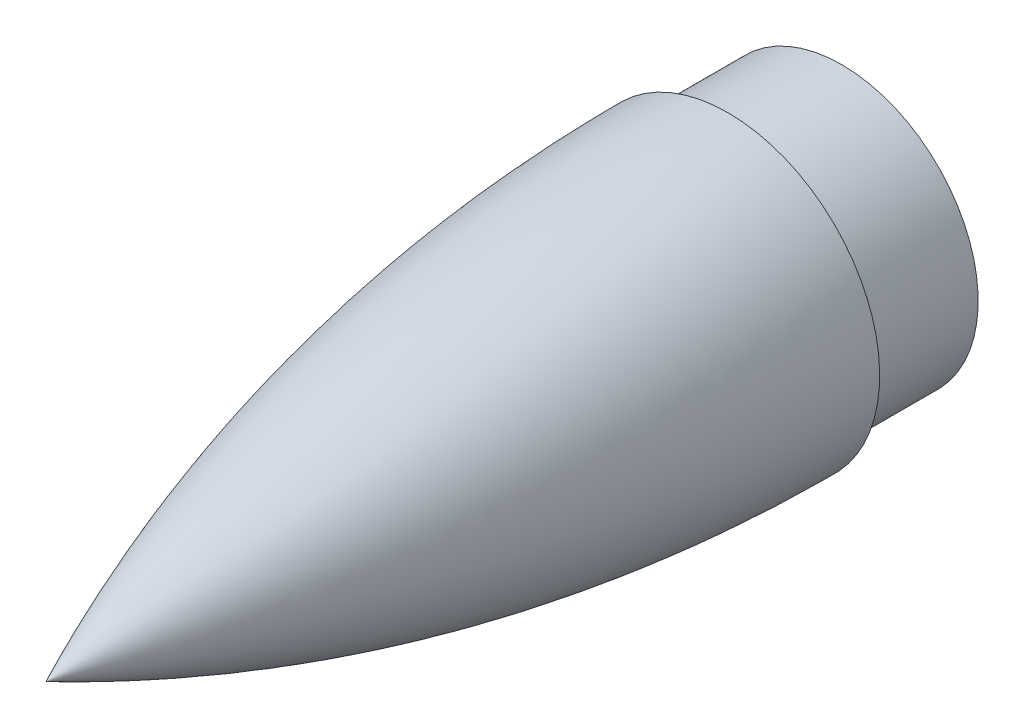
SolidWorks part; units mm, degrees
ref_plane "Front Plane" through (0, 0, 0) normal (0, 0, 1) x (1, 0, 0)
ref_plane "Top Plane" through (0, 0, 0) normal (0, 1, 0) x (1, 0, 0)
ref_plane "Right Plane" through (0, 0, 0) normal (1, 0, 0) x (0, 0, -1)
sketch "Sketch2" plane through (0, 0, 0) normal (1, 0, 0) x (0, 0, -1)
  line L0 (90, 20) -> (90, 18)
  line L1 (90, 18) -> (105, 18)
  line L2 (105, 18) -> (105, 0)
  line L3 (105, 0) -> (0, 0)
  spline S0 degree 9 poles (-8.3054, -4.106) (3.6174, 2.1154) (15.5403, 7.2569) (27.4631, 11.4557) (39.3859, 14.791) (51.3087, 17.3172) (63.2315, 19.0687) (75.1544, 20.0656) (87.0772, 20.3147) (99, 19.8093) knots 0 0 0 0 0 0 0 0 0 0 1 1 1 1 1 1 1 1 1 1 construction
  spline S1 degree 9 poles (0, 0) (10, 4.6753) (20, 8.6385) (30, 11.9562) (40, 14.6719) (50, 16.8168) (60, 18.4118) (70, 19.4706) (80, 20) (90, 20) knots 0.0774 0.0774 0.0774 0.0774 0.0774 0.0774 0.0774 0.0774 0.0774 0.0774 0.916127 0.916127 0.916127 0.916127 0.916127 0.916127 0.916127 0.916127 0.916127 0.916127
  dimension "D1" = 105
  dimension "D2" = 90
  dimension "D3" = 18
revolve "Revolve1" add sketch "Sketch2" angle 360 about L3
